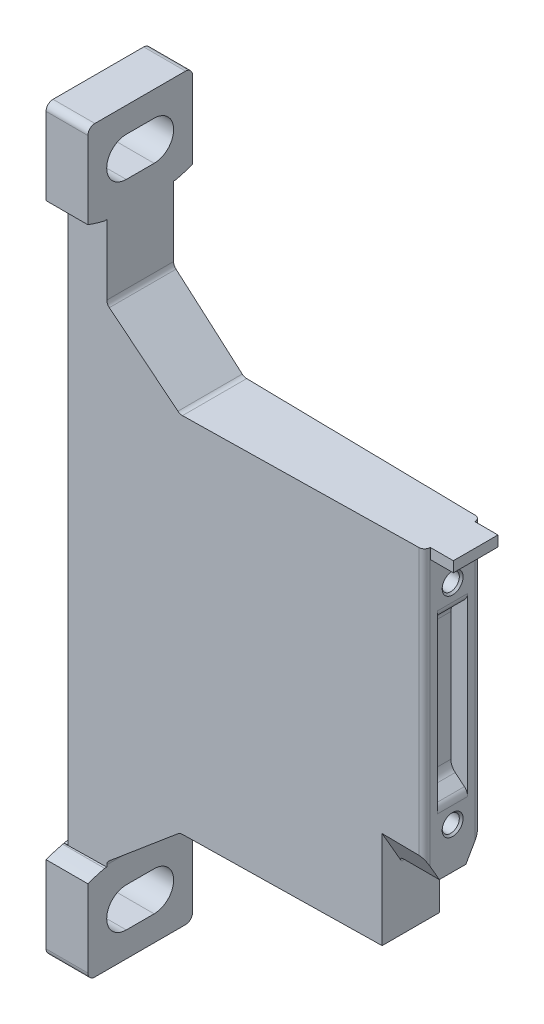
SolidWorks part; units mm, degrees
ref_plane "Front Plane" through (0, 0, 0) normal (0, 0, 1) x (1, 0, 0)
ref_plane "Top Plane" through (0, 0, 0) normal (0, 1, 0) x (1, 0, 0)
ref_plane "Right Plane" through (0, 0, 0) normal (1, 0, 0) x (0, 0, -1)
ref_plane "Plane1" through (0, 0, 0) normal (1, 0, 0) x (0, 0, -1)
sketch "Sketch1" plane through (0, 0, 0) normal (1, 0, 0) x (0, 0, -1)
  line L0 (-7.5, 105) -> (-7.5, 93.9179)
  line L1 (-5, 93.1757) -> (-5, 12.8243)
  line L2 (-7.5, 12.0821) -> (-7.5, 1)
  line L3 (-6.5, 0) -> (6.5, 0)
  line L4 (7.5, 1) -> (7.5, 12.0821)
  line L5 (5, 12.8243) -> (5, 93.1757)
  line L6 (7.5, 93.9179) -> (7.5, 105)
  line L7 (6.5, 106) -> (-6.5, 106)
  arc A0 (-7.5, 93.9179) -> (-5, 93.1757) centre (0, 114.6) ccw
  arc A1 (-5, 12.8243) -> (-7.5, 12.0821) centre (0, -8.6) ccw
  arc A2 (-7.5, 1) -> (-6.5, 0) centre (-6.5, 1) ccw
  arc A3 (6.5, 0) -> (7.5, 1) centre (6.5, 1) ccw
  arc A4 (7.5, 12.0821) -> (5, 12.8243) centre (0, -8.6) ccw
  arc A5 (5, 93.1757) -> (7.5, 93.9179) centre (0, 114.6) ccw
  arc A6 (7.5, 105) -> (6.5, 106) centre (6.5, 105) ccw
  arc A7 (-6.5, 106) -> (-7.5, 105) centre (-6.5, 105) ccw
extrude "Boss-Extrude1" add sketch "Sketch1" along normal blind 51
ref_plane "Plane2" through (0, 0, 0) normal (0, 0, 1) x (1, 0, 0)
sketch "Sketch2" plane through (0, 0, 0) normal (0, 0, 1) x (1, 0, 0)
  line L0 (6, 155.065) -> (6, 83.209)
  line L1 (6.3572, 82.443) -> (16.0212, 74.334)
  line L2 (16.664, 74.1) -> (95, 74.1)
  line L3 (95, 74.1) -> (95, 32.2)
  line L4 (95, 32.2) -> (45.8, 32.2)
  line L5 (44.8, 31.2) -> (44.8, 22.1)
  line L6 (44.8, 22.1) -> (16.664, 22.1)
  line L7 (16.0212, 21.866) -> (6.2858, 13.6971)
  line L8 (6, 13.0842) -> (6, -150)
  line L9 (6, -150) -> (100, -150)
  line L10 (100, -150) -> (100, 155.065)
  line L11 (100, 155.065) -> (6, 155.065)
  arc A0 (6, 83.209) -> (6.3572, 82.443) centre (7, 83.209) ccw
  arc A1 (16.0212, 74.334) -> (16.664, 74.1) centre (16.664, 75.1) ccw
  arc A2 (45.8, 32.2) -> (44.8, 31.2) centre (45.8, 31.2) ccw
  arc A3 (16.664, 22.1) -> (16.0212, 21.866) centre (16.664, 21.1) ccw
  arc A4 (6.2858, 13.6971) -> (6, 13.0842) centre (6.8, 13.0842) ccw
extrude "Cut-Extrude1" cut sketch "Sketch2" against normal blind 10 and the other way blind 10
ref_plane "Plane3" through (0, 0, 0) normal (1, 0, 0) x (0, 0, -1)
sketch "Sketch3" plane through (0, 0, 0) normal (1, 0, 0) x (0, 0, -1)
  line L0 (-2, 3.6) -> (2, 3.6)
  line L1 (2, 9.2) -> (-2, 9.2)
  arc A0 (-2, 9.2) -> (-2, 3.6) centre (-2, 6.4) ccw
  arc A1 (2, 3.6) -> (2, 9.2) centre (2, 6.4) ccw
extrude "Cut-Extrude2" cut sketch "Sketch3" against normal blind 10 and the other way blind 10
ref_plane "Plane4" through (0, 0, 0) normal (1, 0, 0) x (0, 0, -1)
sketch "Sketch4" plane through (0, 0, 0) normal (1, 0, 0) x (0, 0, -1)
  line L0 (-2, 96.8) -> (2, 96.8)
  line L1 (2, 102.4) -> (-2, 102.4)
  arc A0 (-2, 102.4) -> (-2, 96.8) centre (-2, 99.6) ccw
  arc A1 (2, 96.8) -> (2, 102.4) centre (2, 99.6) ccw
extrude "Cut-Extrude3" cut sketch "Sketch4" against normal blind 10 and the other way blind 10
ref_plane "Plane5" through (0, 0, 0) normal (1, 0, 0) x (0, 0, -1)
sketch "Sketch5" plane through (0, 0, 0) normal (1, 0, 0) x (0, 0, -1)
  line L0 (-8, 94.1061) -> (-8, 11.8939)
  line L1 (8, 11.8939) -> (8, 94.1061)
  arc A0 (-8, 11.8939) -> (8, 11.8939) centre (0, -8.6) cw
  arc A1 (8, 94.1061) -> (-8, 94.1061) centre (0, 114.6) cw
extrude "Cut-Extrude4" cut sketch "Sketch5" against normal blind 0.5 and the other way blind 0.5
ref_plane "Plane6" through (0, 12.8, 0) normal (0, 1, 0) x (1, 0, 0)
sketch "Sketch6" plane through (0, 12.8, 0) normal (0, 1, 0) x (1, 0, 0)
  line L0 (-7.8333, -20.4458) -> (56.7096, -20.4458)
  line L1 (56.7096, -20.4458) -> (56.7096, 14.6041)
  line L2 (56.7096, 14.6041) -> (-7.8333, 14.6041)
  line L3 (-7.8333, 14.6041) -> (-7.8333, 5.0295)
  line L4 (-7.8333, 5.0295) -> (50.014, 4.0197)
  line L5 (50.8, 3.2199) -> (50.8, -3.2199)
  line L6 (50.014, -4.0197) -> (-7.8333, -5.0295)
  line L7 (-7.8333, -5.0295) -> (-7.8333, -20.4458)
  arc A0 (50.014, 4.0197) -> (50.8, 3.2199) centre (50, 3.2199) cw
  arc A1 (50.8, -3.2199) -> (50.014, -4.0197) centre (50, -3.2199) cw
extrude "Cut-Extrude5" cut sketch "Sketch6" along normal blind 80.4
ref_plane "Plane7" through (0, 0, 0) normal (0, 0, 1) x (1, 0, 0)
sketch "Sketch7" plane through (0, 0, 0) normal (0, 0, 1) x (1, 0, 0)
  line L0 (-49.7964, 97.0628) -> (-49.7964, 8.9372)
  line L1 (-49.7964, 8.9372) -> (3.5, 13.6)
  line L2 (3.5, 13.6) -> (14.8981, 23.1642)
  line L3 (17.4693, 24.1) -> (40.8, 24.1)
  line L4 (42.8, 26.1) -> (42.8, 32.2)
  line L5 (44.8, 34.2) -> (45.3, 34.2)
  line L6 (45.8, 34.7) -> (45.8, 42.9076)
  line L7 (43.8872, 44.9057) -> (-0.5, 46.8437)
  line L8 (-0.5, 46.8437) -> (-0.5, 49.3563)
  line L9 (-0.5, 49.3563) -> (43.8872, 51.2943)
  line L10 (45.8, 53.2924) -> (45.8, 70.1)
  line L11 (43.8, 72.1) -> (16.3967, 72.1)
  line L12 (13.8256, 73.0358) -> (3.5, 81.7)
  line L13 (3.5, 81.7) -> (3.5, 92.4)
  line L14 (3.5, 92.4) -> (-49.7964, 97.0628)
  arc A0 (14.8981, 23.1642) -> (17.4693, 24.1) centre (17.4693, 20.1) cw
  arc A1 (40.8, 24.1) -> (42.8, 26.1) centre (40.8, 26.1) ccw
  arc A2 (42.8, 32.2) -> (44.8, 34.2) centre (44.8, 32.2) cw
  arc A3 (45.3, 34.2) -> (45.8, 34.7) centre (45.3, 34.7) ccw
  arc A4 (45.8, 42.9076) -> (43.8872, 44.9057) centre (43.8, 42.9076) ccw
  arc A5 (43.8872, 51.2943) -> (45.8, 53.2924) centre (43.8, 53.2924) ccw
  arc A6 (45.8, 70.1) -> (43.8, 72.1) centre (43.8, 70.1) ccw
  arc A7 (16.3967, 72.1) -> (13.8256, 73.0358) centre (16.3967, 76.1) cw
extrude "Cut-Extrude6" cut sketch "Sketch7" against normal blind 1.5 and the other way blind 1.5
ref_plane "Plane8" through (0, 0, 0) normal (0, 0, 1) x (1, 0, 0)
sketch "Sketch8" plane through (0, 0, 0) normal (0, 0, 1) x (1, 0, 0)
  line L0 (50.3, 72.6) -> (54.1, 72.6)
  line L1 (54.1, 72.6) -> (54.1, 74.1)
  line L2 (54.1, 74.1) -> (50.3, 74.1)
  line L3 (50.3, 74.1) -> (50.3, 72.6)
extrude "Boss-Extrude2" add sketch "Sketch8" against normal blind 3.2 and the other way blind 3.2
ref_plane "Plane9" through (0, 0, 0) normal (0, 0, 1) x (1, 0, 0)
sketch "Sketch9" plane through (0, 0, 0) normal (0, 0, 1) x (1, 0, 0)
  line L0 (48.4, 62.2701) -> (48.4, 43.9299)
  line L1 (49.0251, 42.5893) -> (50.3356, 41.4897)
  line L2 (50.8, 40.4938) -> (55.7133, 36.9773)
  line L3 (55.7133, 36.9773) -> (55.7133, 69.2227)
  line L4 (55.7133, 69.2227) -> (50.8, 65.7062)
  line L5 (50.3356, 64.7103) -> (49.0251, 63.6107)
  arc A0 (48.4, 43.9299) -> (49.0251, 42.5893) centre (50.15, 43.9299) ccw
  arc A1 (50.3356, 41.4897) -> (50.8, 40.4938) centre (49.5, 40.4938) cw
  arc A2 (50.8, 65.7062) -> (50.3356, 64.7103) centre (49.5, 65.7062) cw
  arc A3 (49.0251, 63.6107) -> (48.4, 62.2701) centre (50.15, 62.2701) ccw
extrude "Cut-Extrude7" cut sketch "Sketch9" against normal blind 2.15 and the other way blind 2.15
ref_plane "Plane10" through (0, 0, 0) normal (0, 0, 1) x (1, 0, 0)
sketch "Sketch10" plane through (0, 0, 0) normal (0, 0, 1) x (1, 0, 0)
  line L0 (45.8, 68.1) -> (45.8, 69.6)
  line L1 (45.8, 69.6) -> (46.0705, 69.3295)
  line L2 (46.0705, 69.3295) -> (50.5295, 69.3295)
  line L3 (50.5295, 69.3295) -> (50.8, 69.6)
  line L4 (50.8, 69.6) -> (50.8, 68.1)
  line L5 (50.8, 68.1) -> (45.8, 68.1)
  line L6 (50.8, 68.1) -> (45.8, 68.1) construction
revolve "Cut-Revolve1" cut sketch "Sketch10" angle 360 about L6
cosmetic thread "Cosmetic Thread1" parameters "D1"=5, "D2"=3
ref_plane "Plane11" through (0, 0, 0) normal (0, 0, 1) x (1, 0, 0)
sketch "Sketch11" plane through (0, 0, 0) normal (0, 0, 1) x (1, 0, 0)
  line L0 (45.8, 38.1) -> (45.8, 39.6)
  line L1 (45.8, 39.6) -> (46.0705, 39.3295)
  line L2 (46.0705, 39.3295) -> (50.5295, 39.3295)
  line L3 (50.5295, 39.3295) -> (50.8, 39.6)
  line L4 (50.8, 39.6) -> (50.8, 38.1)
  line L5 (50.8, 38.1) -> (45.8, 38.1)
  line L6 (50.8, 38.1) -> (45.8, 38.1) construction
revolve "Cut-Revolve2" cut sketch "Sketch11" angle 360 about L6
cosmetic thread "Cosmetic Thread2" parameters "D1"=5, "D2"=3
ref_plane "Plane12" through (50.8, 0, 0) normal (1, 0, 0) x (0, 0, -1)
sketch "Sketch12" plane through (50.8, 0, 0) normal (1, 0, 0) x (0, 0, -1)
  line L0 (-16.0833, 30.7) -> (16.9167, 30.7)
  line L1 (16.9167, 30.7) -> (16.9167, 58.2097)
  line L2 (16.9167, 58.2097) -> (1.3226, 31.2)
  line L3 (1.3226, 31.2) -> (-1.3226, 31.2)
  line L4 (-1.3226, 31.2) -> (-16.0833, 56.7662)
  line L5 (-16.0833, 56.7662) -> (-16.0833, 30.7)
extrude "Cut-Extrude8" cut sketch "Sketch12" against normal blind 6 and the other way blind 6
